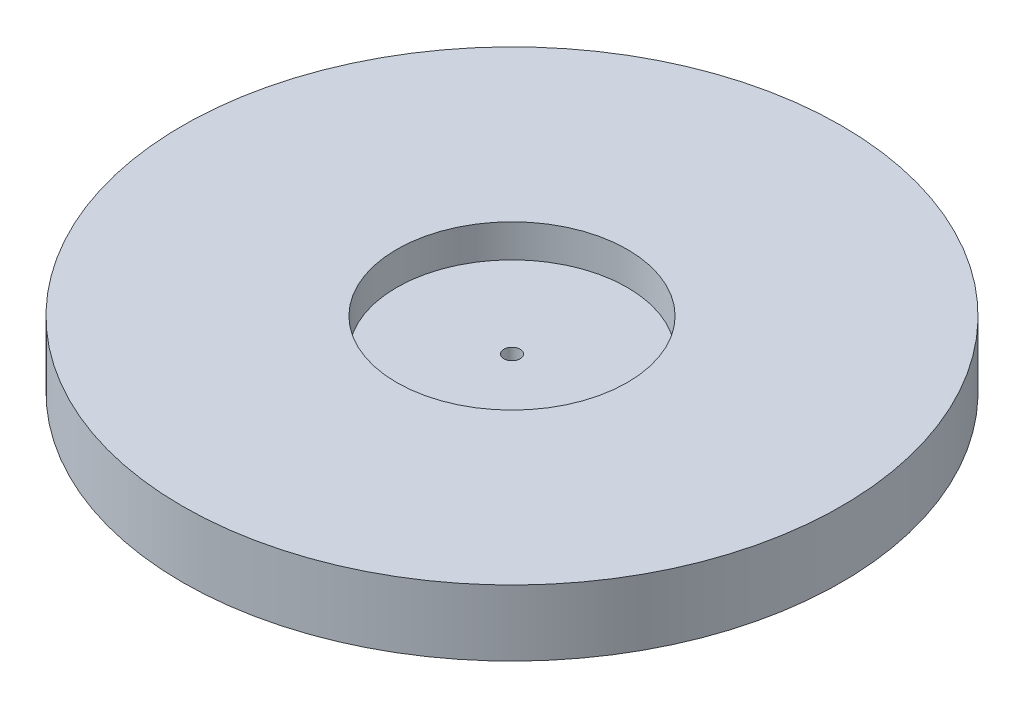
SolidWorks part; units mm, degrees
ref_plane "Front Plane" through (0, 0, 0) normal (0, 0, 1) x (1, 0, 0)
ref_plane "Top Plane" through (0, 0, 0) normal (0, 1, 0) x (1, 0, 0)
ref_plane "Right Plane" through (0, 0, 0) normal (1, 0, 0) x (0, 0, -1)
sketch "Sketch1" plane through (0, 0, 0) normal (0, 1, 0) x (1, 0, 0)
  circle A0 centre (0, 0) radius 127
  circle A1 centre (0, 0) radius 3.175
  dimension "D1" = 6.35
  dimension "D2" = 254
extrude "Boss-Extrude1" add sketch "Sketch1" along normal blind 25.4
sketch "Sketch3" plane through (0, 25.4, 0) normal (0, 1, 0) x (1, 0, 0)
  circle A0 centre (0, 0) radius 44.45
  dimension "D1" = 88.9
extrude "Cut-Extrude1" cut sketch "Sketch3" against normal blind 12.7
